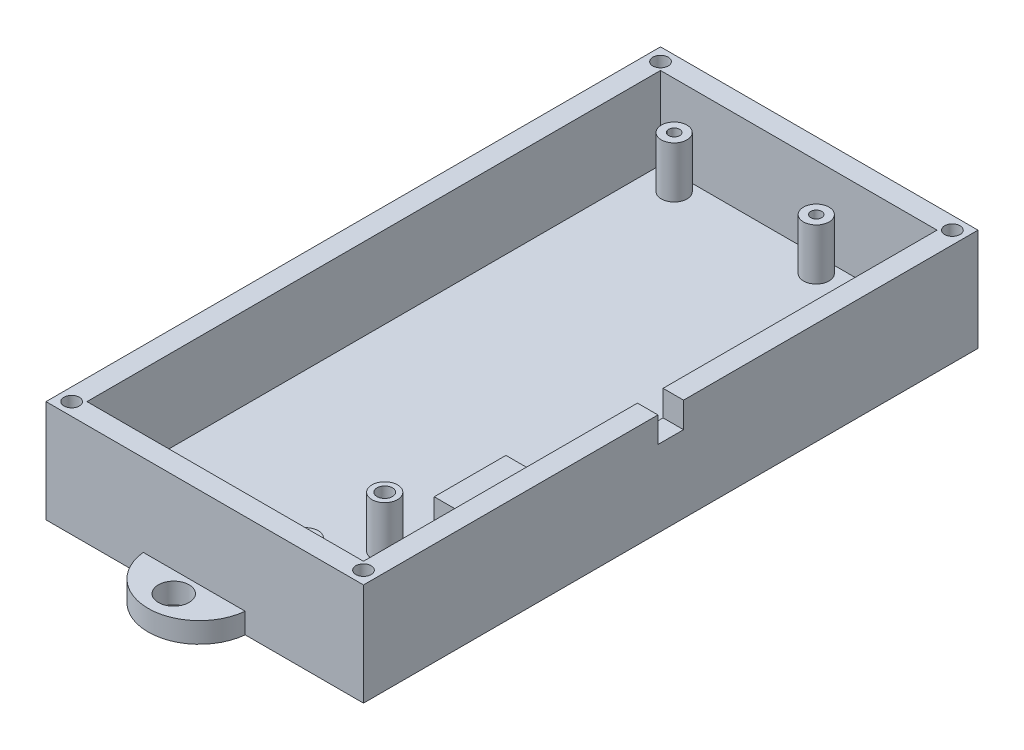
SolidWorks part; units mm, degrees
ref_plane "Front Plane" through (0, 0, 0) normal (0, 0, 1) x (1, 0, 0)
ref_plane "Top Plane" through (0, 0, 0) normal (0, 1, 0) x (1, 0, 0)
ref_plane "Right Plane" through (0, 0, 0) normal (1, 0, 0) x (0, 0, -1)
sketch "Sketch1" plane through (0, 0, 0) normal (0, 1, 0) x (1, 0, 0)
  line L1 (-30, 59) -> (30, 59)
  line L2 (-30, 59) -> (-30, -59)
  line L3 (-30, -59) -> (30, -59)
  line L4 (30, 59) -> (30, -59)
  line L5 (-30, 59) -> (30, -59) construction
  line L6 (-30, -59) -> (30, 59) construction
  point P0 (0, 0)
  dimension "D1" = 118
  dimension "D2" = 60
extrude "Boss-Extrude1" add sketch "Sketch1" along normal blind 4
sketch "Sketch2" plane through (0, 4, 0) normal (0, 1, 0) x (1, 0, 0)
  line L2 (-30, -59) -> (30, -59) construction
  circle A0 centre (-21.1832, 52.8497) radius 2.5
  circle A1 centre (6.5668, 52.8501) radius 2.5
  circle A2 centre (-21.4494, -52.75) radius 2.5
  circle A3 centre (6.3006, -52.75) radius 2.5
  circle A4 centre (11.397, -36.25) radius 2.5
  circle A5 centre (11.4006, -51.75) radius 2.5
  dimension "D1" = 1
  dimension "D4" = 5
  dimension "D2" = 27.75
  dimension "D3" = 105.6
  dimension "6.25" = 6.25
  dimension "D5" = 5.1
  dimension "D6" = 15.5
extrude "Boss-Extrude2" add sketch "Sketch2" along normal blind 10
sketch "Sketch3" plane through (0, 14, 0) normal (0, 1, 0) x (1, 0, 0)
  circle A0 centre (-21.1832, 52.8497) radius 1.075
  circle A1 centre (6.5668, 52.8501) radius 1.075
  circle A2 centre (11.397, -36.25) radius 1.5
  circle A3 centre (11.4006, -51.75) radius 1.5
  circle A4 centre (6.3006, -52.75) radius 1.075
  circle A5 centre (-21.4494, -52.75) radius 1.075
  dimension "D1" = 3
  dimension "D2" = 2.15
extrude "Cut-Extrude1" cut sketch "Sketch3" against normal blind 8
sketch "Sketch4" plane through (0, 4, 0) normal (0, 1, 0) x (1, 0, 0)
  line L0 (30, -59) -> (30, 59) construction
  line L1 (12, -13.1847) -> (26, -13.1847)
  line L2 (12, -13.1847) -> (12, -27.1847)
  line L3 (12, -27.1847) -> (26, -27.1847)
  line L4 (26, -13.1847) -> (26, -27.1847)
  line L5 (12, -13.1847) -> (26, -27.1847) construction
  line L6 (12, -27.1847) -> (26, -13.1847) construction
  point P0 (19, -20.1847)
  dimension "D1" = 14
  dimension "D2" = 14
  dimension "D3" = 4
extrude "Boss-Extrude3" add sketch "Sketch4" along normal blind 5
sketch "Sketch5" plane through (0, 4, 0) normal (0, 1, 0) x (1, 0, 0)
  line L1 (-30, 59) -> (30, 59)
  line L2 (-30, 59) -> (-30, -59)
  line L3 (-30, -59) -> (30, -59)
  line L4 (30, 59) -> (30, -59)
  line L5 (-27, 56) -> (27, 56)
  line L6 (-27, 56) -> (-27, -56)
  line L7 (-27, -56) -> (27, -56)
  line L8 (27, 56) -> (27, -56)
  dimension "D1" = 3
  dimension "D2" = 3
  dimension "D3" = 3
  dimension "D4" = 3
extrude "Boss-Extrude4" add sketch "Sketch5" along normal blind 16
sketch "Sketch10" plane through (0, 0, 0) normal (0, 1, 0) x (1, 0, 0)
  line L0 (-30, -59) -> (30, -59) construction
  line L1 (31, -60) -> (-31, -60)
  line L2 (31, -60) -> (31, 60)
  line L3 (31, 60) -> (-31, 60)
  line L4 (-31, -60) -> (-31, 60)
  line L5 (31, -60) -> (-31, 60) construction
  line L6 (31, 60) -> (-31, -60) construction
  line L7 (30, -59) -> (30, 59) construction
  line L9 (-30, 59) -> (30, 59)
  line L10 (-30, 59) -> (-30, -59)
  line L11 (-30, -59) -> (30, -59)
  line L12 (30, 59) -> (30, -59)
  line L13 (-30, 59) -> (30, -59) construction
  line L14 (-30, -59) -> (30, 59) construction
  point P0 (0, 0)
  point P10 (0, 0)
  dimension "D1" = 1
  dimension "D2" = 1
extrude "Boss-Extrude7" add sketch "Sketch10" along normal up to surface (20 mm away) up to face at (0, 20, 0)
sketch "Sketch6" plane through (0, 20, 0) normal (0, 1, 0) x (1, 0, 0)
  line L0 (-30, 59) -> (-30, -59) construction
  line L1 (30, -59) -> (30, 59) construction
  line L2 (30, 59) -> (-30, 59) construction
  line L3 (-30, -59) -> (30, -59) construction
  circle A0 centre (-28.5, 57.5) radius 1.5
  circle A1 centre (28.5, 57.5) radius 1.5
  circle A2 centre (-28.5, -57.5) radius 1.5
  circle A3 centre (28.5, -57.5) radius 1.5
  dimension "3" = 3
  dimension "D1" = 1.5
  dimension "2" = 1.5
  dimension "D2" = 1.5
  dimension "D3" = 1.5
  dimension "D4" = 1.5
  dimension "D5" = 1.5
  dimension "D6" = 1.5
  dimension "D7" = 1.5
extrude "Cut-Extrude2" cut sketch "Sketch6" against normal blind 10
sketch "Sketch7" plane through (30, 0, 0) normal (1, 0, 0) x (0, 0, -1)
  line L0 (-59, 20) -> (59, 20) construction
  line L1 (-2.5, 25) -> (2.5, 25)
  line L2 (-2.5, 25) -> (-2.5, 15)
  line L3 (-2.5, 15) -> (2.5, 15)
  line L4 (2.5, 25) -> (2.5, 15)
  line L5 (-2.5, 25) -> (2.5, 15) construction
  line L6 (-2.5, 15) -> (2.5, 25) construction
  point P0 (0, 20)
  dimension "D1" = 5
  dimension "D2" = 10
extrude "Cut-Extrude3" cut sketch "Sketch7" against normal up to next and the other way blind 10
sketch "Sketch8" plane through (0, 0, 0) normal (0, 1, 0) x (1, 0, 0)
  line L0 (30, 59) -> (-30, 59) construction
  line L1 (10, 59) -> (-10, 59)
  line L2 (7.9466, -59.0033) -> (-12.0534, -59.0033)
  arc A0 (7.9466, -59.0033) -> (-12.0534, -59.0033) centre (-2.0534, -59.0033) cw
  arc A1 (-10, 59) -> (10, 59) centre (0, 59) cw
  circle A2 centre (-2.0534, -64.0033) radius 3
  circle A3 centre (0, 64) radius 3
  dimension "D1" = 10
  dimension "D2" = 10
  dimension "D3" = 6
  dimension "D6" = 6
  dimension "D4" = 5
  dimension "D5" = 5
extrude "Boss-Extrude5" add sketch "Sketch8" along normal blind 4
